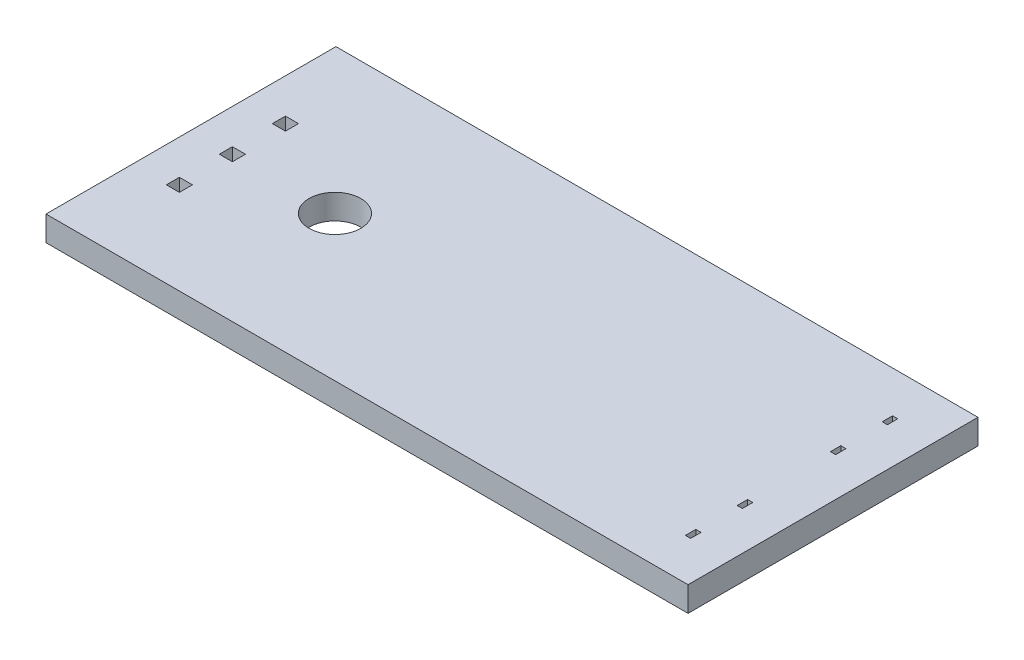
SolidWorks part; units mm, degrees
material "Epoxy, Unfilled"
ref_plane "Front Plane" through (0, 0, 0) normal (0, 0, 1) x (1, 0, 0)
ref_plane "Top Plane" through (0, 0, 0) normal (0, 1, 0) x (1, 0, 0)
ref_plane "Right Plane" through (0, 0, 0) normal (1, 0, 0) x (0, 0, -1)
sketch "Sketch1" plane through (0, 0, 0) normal (0, 1, 0) x (1, 0, 0)
  line L1 (-15.75, -6.6445) -> (15.25, -6.6445)
  line L2 (-15.75, -6.6445) -> (-15.75, 7.3555)
  line L3 (-15.75, 7.3555) -> (15.25, 7.3555)
  line L4 (15.25, -6.6445) -> (15.25, 7.3555)
  line L5 (-15.75, -6.6445) -> (15.25, 7.3555) construction
  line L6 (-15.75, 7.3555) -> (15.25, -6.6445) construction
  point P0 (-0.25, 0.3555)
  dimension "D1" = 14
  dimension "D2" = 31
extrude "Boss-Extrude1" add sketch "Sketch1" along normal blind 1.2
sketch "Sketch2" plane through (0, 1.2, 0) normal (0, 1, 0) x (1, 0, 0)
  line L0 (13.25, -6.6445) -> (13.25, 7.3555) construction
  line L1 (-15.75, -6.6445) -> (15.25, -6.6445) construction
  line L2 (15.25, 7.3555) -> (-15.75, 7.3555) construction
  line L3 (15.25, 0.3555) -> (-15.75, 0.3555) construction
  line L4 (15.25, -6.6445) -> (15.25, 7.3555) construction
  line L5 (-15.75, 7.3555) -> (-15.75, -6.6445) construction
  line L6 (-0.25, -6.6445) -> (-0.25, 7.3555) construction
  line L7 (-13.75, -6.6445) -> (-13.75, 7.3555) construction
  line L8 (-13.435, 3.2305) -> (-13.435, 2.6005)
  line L9 (-13.435, 0.0405) -> (-14.065, 0.0405)
  line L10 (-13.435, 0.0405) -> (-13.435, 0.6705)
  line L11 (-13.435, 0.6705) -> (-14.065, 0.6705)
  line L12 (-14.065, 0.0405) -> (-14.065, 0.6705)
  line L13 (-13.435, 0.0405) -> (-14.065, 0.6705) construction
  line L14 (-13.435, 0.6705) -> (-14.065, 0.0405) construction
  line L15 (-13.435, -2.5195) -> (-14.065, -2.5195)
  line L16 (-13.435, -2.5195) -> (-13.435, -1.8895)
  line L17 (-13.435, -1.8895) -> (-14.065, -1.8895)
  line L18 (-14.065, -2.5195) -> (-14.065, -1.8895)
  line L19 (-13.435, -2.5195) -> (-14.065, -1.8895) construction
  line L20 (-13.435, -1.8895) -> (-14.065, -2.5195) construction
  line L21 (-13.435, 3.2305) -> (-14.065, 3.2305)
  line L22 (-14.065, 3.2305) -> (-14.065, 2.6005)
  line L23 (-13.435, 2.6005) -> (-14.065, 2.6005)
  line L24 (13.375, 2.3555) -> (13.125, 2.8555) construction
  line L25 (13.125, -4.6445) -> (13.375, -4.6445)
  line L26 (13.125, -4.6445) -> (13.125, -4.1445)
  line L27 (13.125, -4.1445) -> (13.375, -4.1445)
  line L28 (13.375, -4.6445) -> (13.375, -4.1445)
  line L29 (13.125, -4.6445) -> (13.375, -4.1445) construction
  line L30 (13.125, -4.1445) -> (13.375, -4.6445) construction
  line L31 (13.375, -2.1445) -> (13.125, -2.1445)
  line L32 (13.375, -2.1445) -> (13.375, -1.6445)
  line L33 (13.375, -1.6445) -> (13.125, -1.6445)
  line L34 (13.125, -2.1445) -> (13.125, -1.6445)
  line L35 (13.375, -2.1445) -> (13.125, -1.6445) construction
  line L36 (13.375, -1.6445) -> (13.125, -2.1445) construction
  line L37 (13.375, 2.8555) -> (13.125, 2.3555) construction
  line L38 (13.125, 4.8555) -> (13.375, 5.3555) construction
  line L39 (13.125, 5.3555) -> (13.375, 4.8555) construction
  line L40 (13.125, 2.8555) -> (13.125, 2.3555)
  line L41 (13.375, 2.3555) -> (13.125, 2.3555)
  line L42 (13.375, 2.8555) -> (13.375, 2.3555)
  line L43 (13.375, 2.8555) -> (13.125, 2.8555)
  line L44 (13.375, 5.3555) -> (13.375, 4.8555)
  line L45 (13.125, 4.8555) -> (13.375, 4.8555)
  line L46 (13.125, 5.3555) -> (13.125, 4.8555)
  line L47 (13.125, 5.3555) -> (13.375, 5.3555)
  circle A7 centre (-8.8, 0.3555) radius 1.25
  point P6 (13.25, -4.3945)
  point P17 (13.25, -1.8945)
  point P24 (-13.75, 0.3555)
  point P25 (-13.75, 0.3555)
  point P30 (-13.75, -2.2045)
  point P33 (-10.05, 0.3555)
  point P52 (13.25, 2.6055)
  point P53 (13.25, 5.1055)
  dimension "D1" = 0.5
  dimension "D5" = 2.56
  dimension "D6" = 2.5
  dimension "D2" = 0.25
  dimension "D3" = 2
  dimension "D4" = 2
  dimension "D7" = 5.7
  dimension "D8" = 0.63
  dimension "D9" = 2
extrude "Cut-Extrude1" cut sketch "Sketch2" against normal through all
